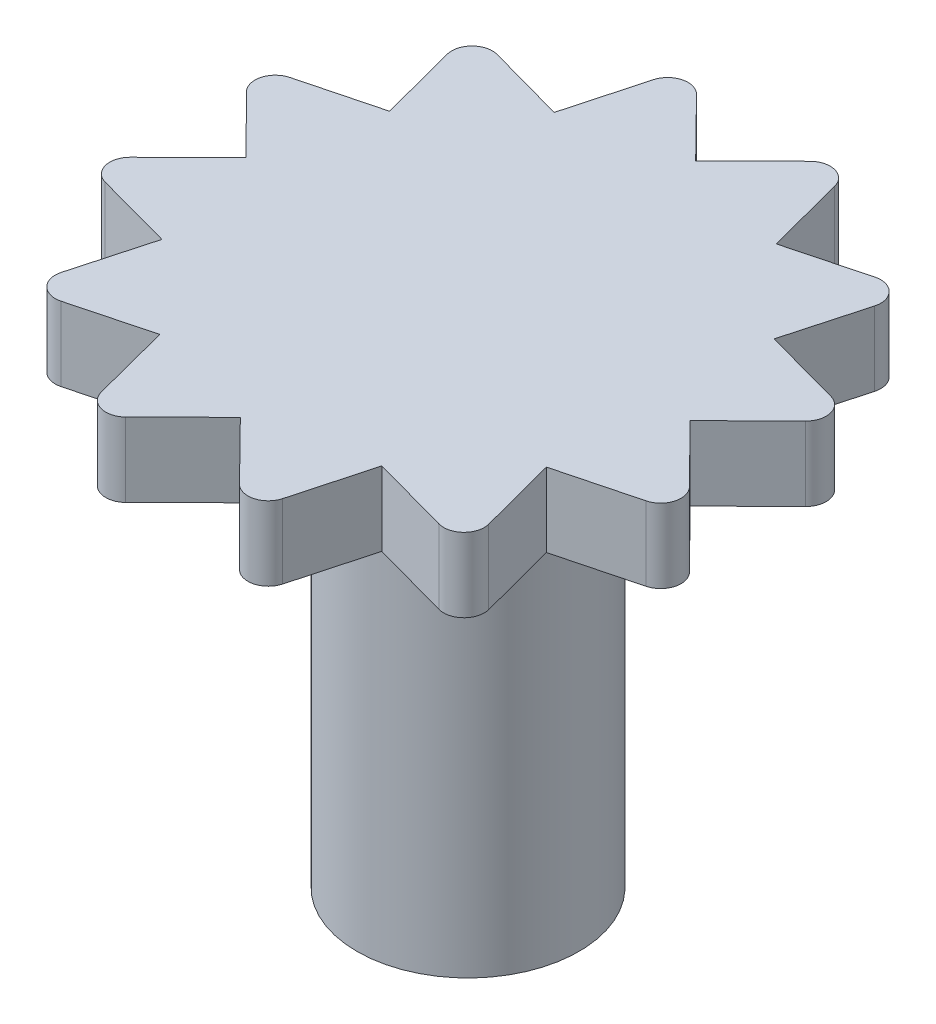
SolidWorks part; units mm, degrees
ref_plane "Front Plane" through (0, 0, 0) normal (0, 0, 1) x (1, 0, 0)
ref_plane "Top Plane" through (0, 0, 0) normal (0, 1, 0) x (1, 0, 0)
ref_plane "Right Plane" through (0, 0, 0) normal (1, 0, 0) x (0, 0, -1)
sketch "Sketch1" plane through (0, 0, 0) normal (0, 1, 0) x (1, 0, 0)
  line L0 (0.0382, 3.0378) -> (0.8163, 3.809)
  line L1 (1.274, 3.6801) -> (1.5519, 2.6117)
  line L3 (1.5519, 2.6117) -> (2.6114, 2.8906)
  line L4 (2.9434, 2.55) -> (2.6499, 1.4859)
  line L5 (2.6499, 1.4859) -> (3.7068, 1.1976)
  line L6 (3.8241, 0.7367) -> (3.0378, -0.0382)
  line L7 (3.0378, -0.0382) -> (3.809, -0.8163)
  line L8 (3.6801, -1.274) -> (2.6117, -1.5519)
  line L9 (2.6117, -1.5519) -> (2.8906, -2.6114)
  line L10 (2.55, -2.9434) -> (1.4859, -2.6499)
  line L11 (1.4859, -2.6499) -> (1.1976, -3.7068)
  line L12 (0.7367, -3.8241) -> (-0.0382, -3.0378)
  line L13 (-0.0382, -3.0378) -> (-0.8163, -3.809)
  line L14 (-1.274, -3.6801) -> (-1.5519, -2.6117)
  line L15 (-1.5519, -2.6117) -> (-2.6114, -2.8906)
  line L16 (-2.9434, -2.55) -> (-2.6499, -1.4859)
  line L17 (-2.6499, -1.4859) -> (-3.7068, -1.1976)
  line L18 (-3.8241, -0.7367) -> (-3.0378, 0.0382)
  line L19 (-3.0378, 0.0382) -> (-3.809, 0.8163)
  line L20 (-3.6801, 1.274) -> (-2.6117, 1.5519)
  line L21 (-2.6117, 1.5519) -> (-2.8906, 2.6114)
  line L22 (-2.55, 2.9434) -> (-1.4859, 2.6499)
  line L23 (-1.4859, 2.6499) -> (-1.1976, 3.7068)
  line L24 (-0.7367, 3.8241) -> (0.0382, 3.0378)
  arc A1 (1.274, 3.6801) -> (0.8163, 3.809) centre (1.0075, 3.6107) ccw
  arc A2 (2.9434, 2.55) -> (2.6114, 2.8906) centre (2.6778, 2.6233) ccw
  arc A3 (3.8241, 0.7367) -> (3.7068, 1.1976) centre (3.6307, 0.9329) ccw
  arc A4 (3.6801, -1.274) -> (3.809, -0.8163) centre (3.6107, -1.0075) ccw
  arc A5 (2.55, -2.9434) -> (2.8906, -2.6114) centre (2.6233, -2.6778) ccw
  arc A6 (0.7367, -3.8241) -> (1.1976, -3.7068) centre (0.9329, -3.6307) ccw
  arc A7 (-1.274, -3.6801) -> (-0.8163, -3.809) centre (-1.0075, -3.6107) ccw
  arc A8 (-2.9434, -2.55) -> (-2.6114, -2.8906) centre (-2.6778, -2.6233) ccw
  arc A9 (-3.8241, -0.7367) -> (-3.7068, -1.1976) centre (-3.6307, -0.9329) ccw
  arc A10 (-3.6801, 1.274) -> (-3.809, 0.8163) centre (-3.6107, 1.0075) ccw
  arc A11 (-2.55, 2.9434) -> (-2.8906, 2.6114) centre (-2.6233, 2.6778) ccw
  arc A12 (-0.7367, 3.8241) -> (-1.1976, 3.7068) centre (-0.9329, 3.6307) ccw
  point P66 (0, 0)
  dimension "D4" = 12
extrude "Boss-Extrude1" add sketch "Sketch1" along normal blind 1 contours L4 L5 A3 L6 L7 A4 L8 L9 A5 L10 L11 A6 L12 L13 A7 L14 L15 A8 L16 L17 A9 L18 L19 A10 L20 L21 A11 L22 L23 A12 L24 L0 A1 L1 L3 A2
sketch "Sketch2" plane through (0, 0, 0) normal (0, -1, 0) x (1, 0, 0)
  circle A0 centre (0, 0) radius 1.5
  dimension "D1" = 3
extrude "Boss-Extrude2" add sketch "Sketch2" along normal blind 6
cosmetic thread "Cosmetic Thread1" parameters "D2"=2
